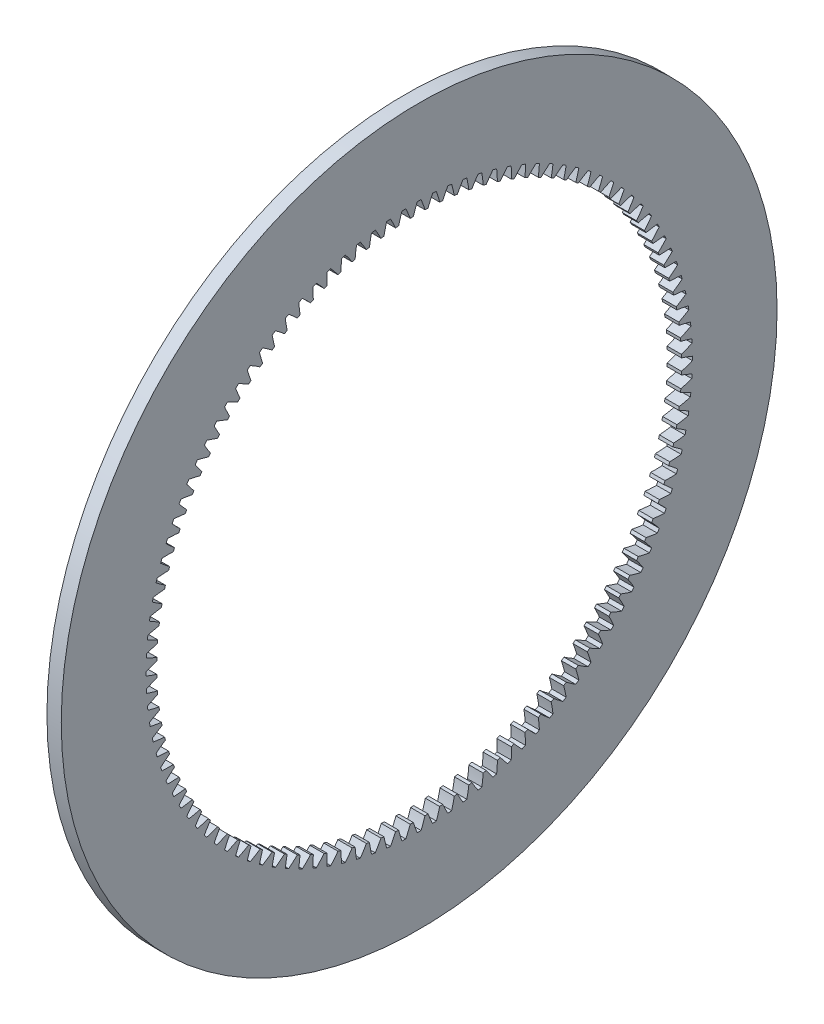
SolidWorks part; units mm, degrees
ref_plane "Plane1" through (0, 0, 0) normal (0, 0, 1) x (1, 0, 0)
ref_plane "Plane2" through (0, 0, 0) normal (0, 1, 0) x (1, 0, 0)
ref_plane "Plane3" through (0, 0, 0) normal (1, 0, 0) x (0, 0, -1)
sketch "HoldingSke" plane through (0, 0, 0) normal (0, 1, 0) x (1, 0, 0)
  line L0 (0, 0) -> (-0.3746, -0.9272)
  line L1 (-15, 0) -> (100, 0) construction
  line L2 (0, 0) -> (-2.1039, 2.3779)
  line L3 (0, 0) -> (-11.863, 4.5341)
  line L4 (0, 0) -> (-3.2351, 8.0072)
  line L5 (0, 0) -> (-23.7986, -8.8762)
  line L6 (0, 0) -> (-10.5278, -7.1032)
  line L7 (-2.1039, 2.3779) -> (3.3635, 27.1825)
  line L8 (-76.2, 3.3779) -> (-54.61, 3.3779)
  line L9 (-71.009, 38.7566) -> (-53.1078, 45.2721)
  line L10 (-76.2, 71.12) -> (104.1128, 71.12)
  line L11 (0, 0) -> (-3, 0)
  line L12 (-76.2, 101.6) -> (-76.162, 101.6)
  line L13 (24.9733, 27.94) -> (52.9518, 28.4284)
  line L14 (24.9733, 27.94) -> (24.9743, 27.94)
  line L15 (24.9733, 27.94) -> (100.4006, 29.5858)
  circle A0 centre (0, 0) radius 75
  circle A1 centre (0, 0) radius 12.7
  circle A2 centre (0, 0) radius 12.7
  dimension "MHD" = 25.4
  dimension "Hub_dia" = 25.4
  dimension "Diameter" = 150
  dimension "Num_teeth" = 112
  dimension "Pitch_radius" = 180.3128
  dimension "Pitch" = 1
  dimension "Width" = 3
  dimension "Overall_len" = 25.4
  dimension "Show_teeth" = 112
  dimension "Thickness" = 12.7
  dimension "OAL" = 25.4001
  dimension "T_dim" = 21.59
  dimension "Ap" = 20
  dimension "H" = 19.05
  dimension "Backlash" = 0.038
  dimension "Addendum_fac" = 1
  dimension "Dedendum_fac" = 1.25
  dimension "Clearance_fac" = 0.25
  dimension "Dedendum_add" = 0.001
  dimension "Module" = 1
sketch "BasProSke" plane through (0, 0, 0) normal (0, 1, 0) x (1, 0, 0)
  line L0 (-10, 0) -> (60, 0) construction
  line L1 (0, 55) -> (0, 75)
  line L2 (0, 55) -> (3, 55)
  line L3 (3, 55) -> (3, 75)
  line L4 (3, 75) -> (0, 75)
  dimension "Diameter" = 150
  dimension "Thickness" = 3
  dimension "Inside_diameter" = 110
revolve "Base-Revolve" add sketch "BasProSke" angle 360 about L0
sketch "TooCutSke" plane through (0, 0, 0) normal (1, 0, 0) x (0, 0, -1)
  line L3 (0.8804, 55.9931) -> (0.8804, 53.6633) construction
  line L4 (0, 0) -> (0, 59.563) construction
  line L5 (0, 0) -> (-1.9163, 68.3006) construction
  line L6 (-25.5195, 46.6631) -> (36.4996, 48.4032) construction
  circle A0 centre (0, 0) radius 56 construction
  circle A1 centre (0, 0) radius 57.251 construction
  circle A2 centre (0, 0) radius 47.3605 construction
  circle A3 centre (0, 0) radius 54.9746 construction
  arc A4 (1.2227, 54.961) -> (0.4021, 57.2496) centre (-25.5195, 46.6631) ccw
  arc A5 (1.2227, 54.961) -> (-1.2227, 54.961) centre (0, 0) ccw
  arc A6 (0.4021, 57.2496) -> (-0.4021, 57.2496) centre (0, 0) ccw
  arc A7 (-0.4021, 57.2496) -> (-1.2227, 54.961) centre (25.5195, 46.6631) ccw
  dimension "Pitch_dia" = 112
  dimension "Base_dia" = 94.721
  dimension "Root_dia" = 114.502
  dimension "Overcut_dia" = 109.9492
  dimension "Flank_rad" = 28
  dimension "Half_ang" = 1.607
  dimension "Half_CT" = 0.8804
extrude "ToothCut" cut sketch "TooCutSke" along normal through all
fillet "Breaks" [suppressed] radius 0.1
fillet "RootFillets" [suppressed] radius 0.251
pattern_circular "TeethCuts" count 112 every 3.214 about axis through (-10, 0, 0) along (1, 0, 0) of "RootFillets", "Breaks", "ToothCut"
equation "' \"Module@HoldingSke\" = 6.35"
equation "' \"Num_teeth@HoldingSke\" = 24"
equation "' \"Ap@HoldingSke\" =  14.5"
equation "' \"Width@HoldingSke\" = 12"
equation "' \"Diameter@HoldingSke\" = 8 * 25.4"
equation "' \"Show_teeth@HoldingSke\" = 100"
equation "' \"Backlash@HoldingSke\" = 0.009 * 25.4"
equation "' \"Addendum_fac@HoldingSke\" = 1.0"
equation "' \"Dedendum_fac@HoldingSke\" = 1.25"
equation "' \"Dedendum_add@HoldingSke\" = 0.00005 * 25.4"
equation "' \"Clearance_fac@HoldingSke\" = 0.25"
equation "\"Pitch@HoldingSke\" = 1 / \"Module@HoldingSke\" "
equation "\"Overcut_dia@TooCutSke\" = (\"Num_teeth@HoldingSke\" - 2 * \"Addendum_fac@HoldingSke\") / \"Pitch@HoldingSke\" - 0.002 * 25.4"
equation "\"Pitch_dia@TooCutSke\" = \"Num_teeth@HoldingSke\" / \"Pitch@HoldingSke\""
equation "\"Base_dia@TooCutSke\" = \"Num_teeth@HoldingSke\" / \"Pitch@HoldingSke\" * cos((\"Ap@HoldingSke\"  * 3.14159265 / 180)) * 0.90"
equation "\"Root_dia@TooCutSke\" = \"Num_teeth@HoldingSke\"  / \"Pitch@HoldingSke\" + 2 *  \"Dedendum_fac@HoldingSke\"/ \"Pitch@HoldingSke\" + \"Dedendum_add@HoldingSke\" * 2"
equation "\"Half_ang@TooCutSke\" = 180 / \"Num_teeth@HoldingSke\""
equation "\"Half_CT@TooCutSke\" = \"Num_teeth@HoldingSke\" / \"Pitch@HoldingSke\" * sin((3.14159265 / 2 / \"Num_teeth@HoldingSke\")) / 2 + 10 * \"Backlash@HoldingSke\" / 4"
equation "\"Flank_rad@TooCutSke\" = \"Num_teeth@HoldingSke\" / \"Pitch@HoldingSke\" / 4"
equation "\"Radius@RootFillets\"= \"Clearance_fac@HoldingSke\" / \"Pitch@HoldingSke\" + \"Dedendum_add@HoldingSke\""
equation "\"Break_rad@Breaks\" = 0.02 / \"Pitch@HoldingSke\" * 5"
equation "\"Num_teeth@TeethCuts\" = int( \"Show_teeth@HoldingSke\" ) + 1"
equation "\"Num_teeth@TeethCuts\" = ((sgn( \"Num_teeth@TeethCuts\" - \"Num_teeth@HoldingSke\" )-1)*( \"Num_teeth@TeethCuts\" - \"Num_teeth@HoldingSke\" ))/-2+ \"Num_teeth@HoldingSke\""
equation "\"Num_teeth@TeethCuts\" = ((sgn( \"Num_teeth@TeethCuts\" - 2.0)+1)*( \"Num_teeth@TeethCuts\" - 2.0))/2 +2.0"
equation "\"Angle@TeethCuts\" = 360.0 / \"Num_teeth@HoldingSke\""
equation "\"Diameter@BasProSke\" = \"Num_teeth@HoldingSke\"  / \"Pitch@HoldingSke\" + 2 *  \"Dedendum_fac@HoldingSke\"/ \"Pitch@HoldingSke\" + \"Dedendum_add@HoldingSke\" * 2 + 0.002 * 25.4"
equation "\"Diameter@BasProSke\" = ((sgn( \"Diameter@BasProSke\"  - \"Diameter@HoldingSke\" )+1)*( \"Diameter@BasProSke\"  - \"Diameter@HoldingSke\" ))/2 + \"Diameter@HoldingSke\""
equation "\"Inside_diameter@BasProSke\" =  (\"Num_teeth@HoldingSke\" - 2 * \"Addendum_fac@HoldingSke\") / \"Pitch@HoldingSke\" "
equation "\"Thickness@BasProSke\"  = \"Width@HoldingSke\""
